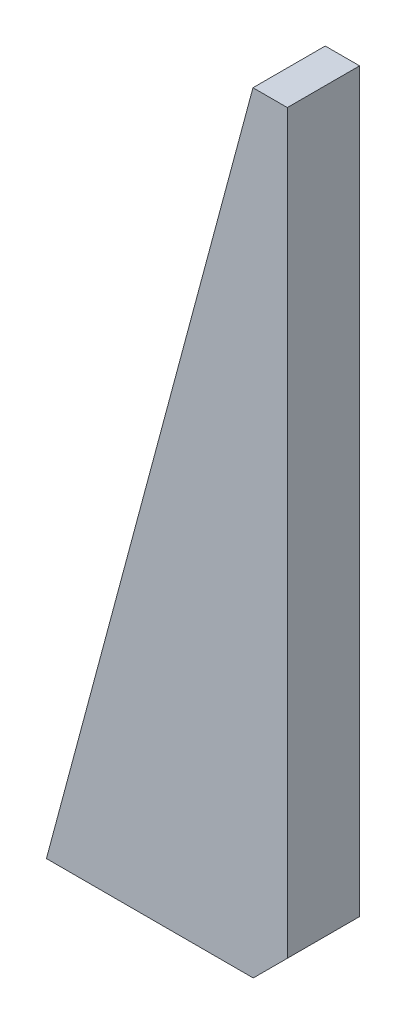
SolidWorks part; units mm, degrees
ref_plane "Front Plane" through (0, 0, 0) normal (0, 0, 1) x (1, 0, 0)
ref_plane "Top Plane" through (0, 0, 0) normal (0, 1, 0) x (1, 0, 0)
ref_plane "Right Plane" through (0, 0, 0) normal (1, 0, 0) x (0, 0, -1)
sketch "Sketch1" plane through (0, 0, 0) normal (0, 0, 1) x (1, 0, 0)
  line L0 (-137.2385, 0) -> (136.4101, 0) construction
  line L1 (0, 214.8137) -> (0, -97.8895) construction
  line L5 (-50, 0) -> (-7.0711, 0)
  line L6 (-7.0711, 0) -> (0, 7.0711)
  line L7 (0, 160) -> (0, 7.0711)
  line L8 (-50, 0) -> (-7.1281, 160)
  line L9 (-7.1281, 160) -> (0, 160)
  point P6 (1.746, 183.888)
  dimension "D1" = 50
  dimension "D2" = 75
  dimension "D3" = 10
  dimension "D4" = 45
  dimension "D5" = 160
extrude "Boss-Extrude1" add sketch "Sketch1" against normal blind 15
